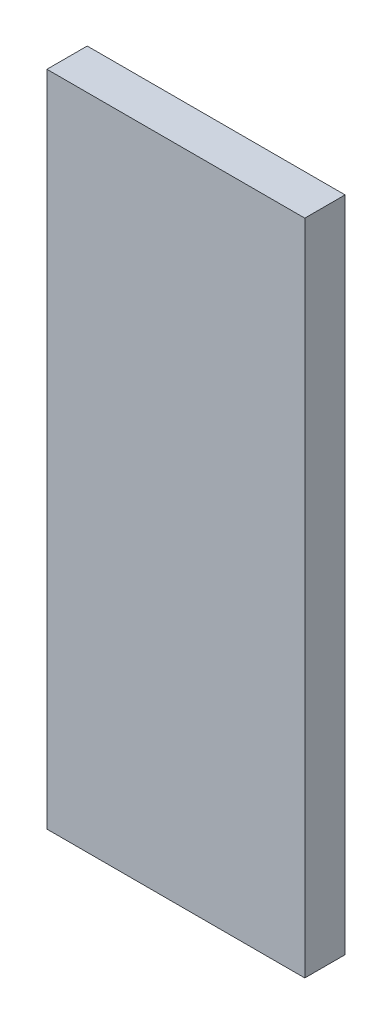
SolidWorks part; units mm, degrees
material "Pine"
ref_plane "Front Plane" through (0, 0, 0) normal (0, 0, 1) x (1, 0, 0)
ref_plane "Top Plane" through (0, 0, 0) normal (0, 1, 0) x (1, 0, 0)
ref_plane "Right Plane" through (0, 0, 0) normal (1, 0, 0) x (0, 0, -1)
sketch "Sketch1" plane through (0, 0, 0) normal (0, 1, 0) x (1, 0, 0)
  line L1 (-48, -7.5) -> (48, -7.5)
  line L2 (-48, -7.5) -> (-48, 7.5)
  line L3 (-48, 7.5) -> (48, 7.5)
  line L4 (48, -7.5) -> (48, 7.5)
  line L5 (-48, -7.5) -> (48, 7.5) construction
  line L6 (-48, 7.5) -> (48, -7.5) construction
  point P0 (0, 0)
  dimension "D1" = 96
  dimension "D2" = 15
extrude "Boss-Extrude1" add sketch "Sketch1" along normal blind 245
